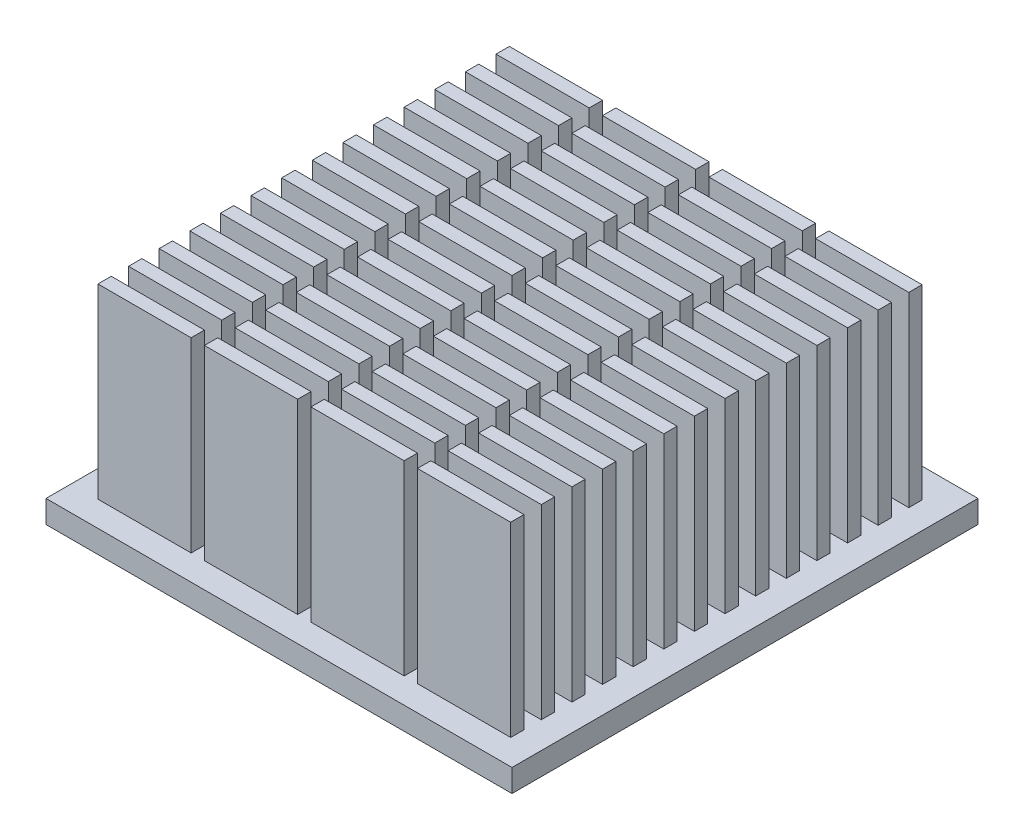
SolidWorks part; units mm, degrees
ref_plane "Front Plane" through (0, 0, 0) normal (0, 0, 1) x (1, 0, 0)
ref_plane "Top Plane" through (0, 0, 0) normal (0, 1, 0) x (1, 0, 0)
ref_plane "Right Plane" through (0, 0, 0) normal (1, 0, 0) x (0, 0, -1)
sketch "Sketch1" plane through (0, 0, 0) normal (0, 1, 0) x (1, 0, 0)
  line L1 (-17.5, -17.5) -> (17.5, -17.5)
  line L2 (-17.5, -17.5) -> (-17.5, 17.5)
  line L3 (-17.5, 17.5) -> (17.5, 17.5)
  line L4 (17.5, -17.5) -> (17.5, 17.5)
  line L5 (-17.5, -17.5) -> (17.5, 17.5) construction
  line L6 (-17.5, 17.5) -> (17.5, -17.5) construction
  point P0 (0, 0)
  dimension "D1" = 35
  dimension "D2" = 35
extrude "Boss-Extrude1" add sketch "Sketch1" along normal blind 1.7
sketch "Sketch2" plane through (0, 1.7, 0) normal (0, 1, 0) x (1, 0, 0)
  line L0 (-15.5, -0.8) -> (-8.5, -0.8)
  line L1 (-15.5, 1.5) -> (-8.5, 1.5)
  line L2 (-15.5, 1.5) -> (-15.5, 0.5)
  line L3 (-15.5, 0.5) -> (-8.5, 0.5)
  line L4 (-8.5, 1.5) -> (-8.5, 0.5)
  line L5 (-7.5, 1.5) -> (-0.5, 1.5)
  line L6 (-7.5, 1.5) -> (-7.5, 0.5)
  line L7 (-7.5, 0.5) -> (-0.5, 0.5)
  line L8 (-0.5, 1.5) -> (-0.5, 0.5)
  line L9 (0.5, 1.5) -> (7.5, 1.5)
  line L10 (0.5, 1.5) -> (0.5, 0.5)
  line L11 (0.5, 0.5) -> (7.5, 0.5)
  line L12 (7.5, 1.5) -> (7.5, 0.5)
  line L13 (8.5, 1.5) -> (15.5, 1.5)
  line L14 (8.5, 1.5) -> (8.5, 0.5)
  line L15 (8.5, 0.5) -> (15.5, 0.5)
  line L16 (15.5, 1.5) -> (15.5, 0.5)
  line L17 (-15.5, -0.8) -> (-15.5, -1.8)
  line L18 (-15.5, -1.8) -> (-8.5, -1.8)
  line L19 (-8.5, -0.8) -> (-8.5, -1.8)
  line L20 (-7.5, -0.8) -> (-0.5, -0.8)
  line L21 (-7.5, -0.8) -> (-7.5, -1.8)
  line L22 (-7.5, -1.8) -> (-0.5, -1.8)
  line L23 (-0.5, -0.8) -> (-0.5, -1.8)
  line L24 (0.5, -0.8) -> (7.5, -0.8)
  line L25 (0.5, -0.8) -> (0.5, -1.8)
  line L26 (0.5, -1.8) -> (7.5, -1.8)
  line L27 (7.5, -0.8) -> (7.5, -1.8)
  line L28 (8.5, -0.8) -> (15.5, -0.8)
  line L29 (8.5, -0.8) -> (8.5, -1.8)
  line L30 (8.5, -1.8) -> (15.5, -1.8)
  line L31 (15.5, -0.8) -> (15.5, -1.8)
  line L32 (-15.5, -3.1) -> (-8.5, -3.1)
  line L33 (-15.5, -3.1) -> (-15.5, -4.1)
  line L34 (-15.5, -4.1) -> (-8.5, -4.1)
  line L35 (-8.5, -3.1) -> (-8.5, -4.1)
  line L36 (-7.5, -3.1) -> (-0.5, -3.1)
  line L37 (-7.5, -3.1) -> (-7.5, -4.1)
  line L38 (-7.5, -4.1) -> (-0.5, -4.1)
  line L39 (-0.5, -3.1) -> (-0.5, -4.1)
  line L40 (0.5, -3.1) -> (7.5, -3.1)
  line L41 (0.5, -3.1) -> (0.5, -4.1)
  line L42 (0.5, -4.1) -> (7.5, -4.1)
  line L43 (7.5, -3.1) -> (7.5, -4.1)
  line L44 (8.5, -3.1) -> (15.5, -3.1)
  line L45 (8.5, -3.1) -> (8.5, -4.1)
  line L46 (8.5, -4.1) -> (15.5, -4.1)
  line L47 (15.5, -3.1) -> (15.5, -4.1)
  line L48 (-15.5, -5.4) -> (-8.5, -5.4)
  line L49 (-15.5, -5.4) -> (-15.5, -6.4)
  line L50 (-15.5, -6.4) -> (-8.5, -6.4)
  line L51 (-8.5, -5.4) -> (-8.5, -6.4)
  line L52 (-7.5, -5.4) -> (-0.5, -5.4)
  line L53 (-7.5, -5.4) -> (-7.5, -6.4)
  line L54 (-7.5, -6.4) -> (-0.5, -6.4)
  line L55 (-0.5, -5.4) -> (-0.5, -6.4)
  line L56 (0.5, -5.4) -> (7.5, -5.4)
  line L57 (0.5, -5.4) -> (0.5, -6.4)
  line L58 (0.5, -6.4) -> (7.5, -6.4)
  line L59 (7.5, -5.4) -> (7.5, -6.4)
  line L60 (8.5, -5.4) -> (15.5, -5.4)
  line L61 (8.5, -5.4) -> (8.5, -6.4)
  line L62 (8.5, -6.4) -> (15.5, -6.4)
  line L63 (15.5, -5.4) -> (15.5, -6.4)
  line L64 (-15.5, -7.7) -> (-8.5, -7.7)
  line L65 (-15.5, -7.7) -> (-15.5, -8.7)
  line L66 (-15.5, -8.7) -> (-8.5, -8.7)
  line L67 (-8.5, -7.7) -> (-8.5, -8.7)
  line L68 (-7.5, -7.7) -> (-0.5, -7.7)
  line L69 (-7.5, -7.7) -> (-7.5, -8.7)
  line L70 (-7.5, -8.7) -> (-0.5, -8.7)
  line L71 (-0.5, -7.7) -> (-0.5, -8.7)
  line L72 (0.5, -7.7) -> (7.5, -7.7)
  line L73 (0.5, -7.7) -> (0.5, -8.7)
  line L74 (0.5, -8.7) -> (7.5, -8.7)
  line L75 (7.5, -7.7) -> (7.5, -8.7)
  line L76 (8.5, -7.7) -> (15.5, -7.7)
  line L77 (8.5, -7.7) -> (8.5, -8.7)
  line L78 (8.5, -8.7) -> (15.5, -8.7)
  line L79 (15.5, -7.7) -> (15.5, -8.7)
  line L80 (-15.5, -10) -> (-8.5, -10)
  line L81 (-15.5, -10) -> (-15.5, -11)
  line L82 (-15.5, -11) -> (-8.5, -11)
  line L83 (-8.5, -10) -> (-8.5, -11)
  line L84 (-7.5, -10) -> (-0.5, -10)
  line L85 (-7.5, -10) -> (-7.5, -11)
  line L86 (-7.5, -11) -> (-0.5, -11)
  line L87 (-0.5, -10) -> (-0.5, -11)
  line L88 (0.5, -10) -> (7.5, -10)
  line L89 (0.5, -10) -> (0.5, -11)
  line L90 (0.5, -11) -> (7.5, -11)
  line L91 (7.5, -10) -> (7.5, -11)
  line L92 (8.5, -10) -> (15.5, -10)
  line L93 (8.5, -10) -> (8.5, -11)
  line L94 (8.5, -11) -> (15.5, -11)
  line L95 (15.5, -10) -> (15.5, -11)
  line L96 (-15.5, -12.3) -> (-8.5, -12.3)
  line L97 (-15.5, -12.3) -> (-15.5, -13.3)
  line L98 (-15.5, -13.3) -> (-8.5, -13.3)
  line L99 (-8.5, -12.3) -> (-8.5, -13.3)
  line L100 (-7.5, -12.3) -> (-0.5, -12.3)
  line L101 (-7.5, -12.3) -> (-7.5, -13.3)
  line L102 (-7.5, -13.3) -> (-0.5, -13.3)
  line L103 (-0.5, -12.3) -> (-0.5, -13.3)
  line L104 (0.5, -12.3) -> (7.5, -12.3)
  line L105 (0.5, -12.3) -> (0.5, -13.3)
  line L106 (0.5, -13.3) -> (7.5, -13.3)
  line L107 (7.5, -12.3) -> (7.5, -13.3)
  line L108 (8.5, -12.3) -> (15.5, -12.3)
  line L109 (8.5, -12.3) -> (8.5, -13.3)
  line L110 (8.5, -13.3) -> (15.5, -13.3)
  line L111 (15.5, -12.3) -> (15.5, -13.3)
  line L112 (-15.5, -14.6) -> (-8.5, -14.6)
  line L113 (-15.5, -14.6) -> (-15.5, -15.6)
  line L114 (-15.5, -15.6) -> (-8.5, -15.6)
  line L115 (-8.5, -14.6) -> (-8.5, -15.6)
  line L116 (-7.5, -14.6) -> (-0.5, -14.6)
  line L117 (-7.5, -14.6) -> (-7.5, -15.6)
  line L118 (-7.5, -15.6) -> (-0.5, -15.6)
  line L119 (-0.5, -14.6) -> (-0.5, -15.6)
  line L120 (0.5, -14.6) -> (7.5, -14.6)
  line L121 (0.5, -14.6) -> (0.5, -15.6)
  line L122 (0.5, -15.6) -> (7.5, -15.6)
  line L123 (7.5, -14.6) -> (7.5, -15.6)
  line L124 (8.5, -14.6) -> (15.5, -14.6)
  line L125 (8.5, -14.6) -> (8.5, -15.6)
  line L126 (8.5, -15.6) -> (15.5, -15.6)
  line L127 (15.5, -14.6) -> (15.5, -15.6)
  line L128 (-15.5, 1.5) -> (-8.5, 1.5)
  line L129 (-15.5, 1.5) -> (-15.5, 0.5)
  line L130 (-15.5, 0.5) -> (-8.5, 0.5)
  line L131 (-8.5, 1.5) -> (-8.5, 0.5)
  line L132 (-7.5, 1.5) -> (-0.5, 1.5)
  line L133 (-7.5, 1.5) -> (-7.5, 0.5)
  line L134 (-7.5, 0.5) -> (-0.5, 0.5)
  line L135 (-0.5, 1.5) -> (-0.5, 0.5)
  line L136 (0.5, 1.5) -> (7.5, 1.5)
  line L137 (0.5, 1.5) -> (0.5, 0.5)
  line L138 (0.5, 0.5) -> (7.5, 0.5)
  line L139 (7.5, 1.5) -> (7.5, 0.5)
  line L140 (8.5, 1.5) -> (15.5, 1.5)
  line L141 (8.5, 1.5) -> (8.5, 0.5)
  line L142 (8.5, 0.5) -> (15.5, 0.5)
  line L143 (15.5, 1.5) -> (15.5, 0.5)
  line L144 (-15.5, -0.8) -> (-8.5, -0.8)
  line L145 (-15.5, -0.8) -> (-15.5, -1.8)
  line L146 (-15.5, -1.8) -> (-8.5, -1.8)
  line L147 (-8.5, -0.8) -> (-8.5, -1.8)
  line L148 (-7.5, -0.8) -> (-0.5, -0.8)
  line L149 (-7.5, -0.8) -> (-7.5, -1.8)
  line L150 (-7.5, -1.8) -> (-0.5, -1.8)
  line L151 (-0.5, -0.8) -> (-0.5, -1.8)
  line L152 (0.5, -0.8) -> (7.5, -0.8)
  line L153 (0.5, -0.8) -> (0.5, -1.8)
  line L154 (0.5, -1.8) -> (7.5, -1.8)
  line L155 (7.5, -0.8) -> (7.5, -1.8)
  line L156 (8.5, -0.8) -> (15.5, -0.8)
  line L157 (8.5, -0.8) -> (8.5, -1.8)
  line L158 (8.5, -1.8) -> (15.5, -1.8)
  line L159 (15.5, -0.8) -> (15.5, -1.8)
  line L160 (-15.5, -3.1) -> (-8.5, -3.1)
  line L161 (-15.5, -3.1) -> (-15.5, -4.1)
  line L162 (-15.5, -4.1) -> (-8.5, -4.1)
  line L163 (-8.5, -3.1) -> (-8.5, -4.1)
  line L164 (-7.5, -3.1) -> (-0.5, -3.1)
  line L165 (-7.5, -3.1) -> (-7.5, -4.1)
  line L166 (-7.5, -4.1) -> (-0.5, -4.1)
  line L167 (-0.5, -3.1) -> (-0.5, -4.1)
  line L168 (0.5, -3.1) -> (7.5, -3.1)
  line L169 (0.5, -3.1) -> (0.5, -4.1)
  line L170 (0.5, -4.1) -> (7.5, -4.1)
  line L171 (7.5, -3.1) -> (7.5, -4.1)
  line L172 (8.5, -3.1) -> (15.5, -3.1)
  line L173 (8.5, -3.1) -> (8.5, -4.1)
  line L174 (8.5, -4.1) -> (15.5, -4.1)
  line L175 (15.5, -3.1) -> (15.5, -4.1)
  line L176 (-15.5, -5.4) -> (-8.5, -5.4)
  line L177 (-15.5, -5.4) -> (-15.5, -6.4)
  line L178 (-15.5, -6.4) -> (-8.5, -6.4)
  line L179 (-8.5, -5.4) -> (-8.5, -6.4)
  line L180 (-7.5, -5.4) -> (-0.5, -5.4)
  line L181 (-7.5, -5.4) -> (-7.5, -6.4)
  line L182 (-7.5, -6.4) -> (-0.5, -6.4)
  line L183 (-0.5, -5.4) -> (-0.5, -6.4)
  line L184 (0.5, -5.4) -> (7.5, -5.4)
  line L185 (0.5, -5.4) -> (0.5, -6.4)
  line L186 (0.5, -6.4) -> (7.5, -6.4)
  line L187 (7.5, -5.4) -> (7.5, -6.4)
  line L188 (8.5, -5.4) -> (15.5, -5.4)
  line L189 (8.5, -5.4) -> (8.5, -6.4)
  line L190 (8.5, -6.4) -> (15.5, -6.4)
  line L191 (15.5, -5.4) -> (15.5, -6.4)
  line L192 (-15.5, -7.7) -> (-8.5, -7.7)
  line L193 (-15.5, -7.7) -> (-15.5, -8.7)
  line L194 (-15.5, -8.7) -> (-8.5, -8.7)
  line L195 (-8.5, -7.7) -> (-8.5, -8.7)
  line L196 (-7.5, -7.7) -> (-0.5, -7.7)
  line L197 (-7.5, -7.7) -> (-7.5, -8.7)
  line L198 (-7.5, -8.7) -> (-0.5, -8.7)
  line L199 (-0.5, -7.7) -> (-0.5, -8.7)
  line L200 (0.5, -7.7) -> (7.5, -7.7)
  line L201 (0.5, -7.7) -> (0.5, -8.7)
  line L202 (0.5, -8.7) -> (7.5, -8.7)
  line L203 (7.5, -7.7) -> (7.5, -8.7)
  line L204 (8.5, -7.7) -> (15.5, -7.7)
  line L205 (8.5, -7.7) -> (8.5, -8.7)
  line L206 (8.5, -8.7) -> (15.5, -8.7)
  line L207 (15.5, -7.7) -> (15.5, -8.7)
  line L208 (-15.5, -10) -> (-8.5, -10)
  line L209 (-15.5, -10) -> (-15.5, -11)
  line L210 (-15.5, -11) -> (-8.5, -11)
  line L211 (-8.5, -10) -> (-8.5, -11)
  line L212 (-7.5, -10) -> (-0.5, -10)
  line L213 (-7.5, -10) -> (-7.5, -11)
  line L214 (-7.5, -11) -> (-0.5, -11)
  line L215 (-0.5, -10) -> (-0.5, -11)
  line L216 (0.5, -10) -> (7.5, -10)
  line L217 (0.5, -10) -> (0.5, -11)
  line L218 (0.5, -11) -> (7.5, -11)
  line L219 (7.5, -10) -> (7.5, -11)
  line L220 (8.5, -10) -> (15.5, -10)
  line L221 (8.5, -10) -> (8.5, -11)
  line L222 (8.5, -11) -> (15.5, -11)
  line L223 (15.5, -10) -> (15.5, -11)
  line L224 (-15.5, -12.3) -> (-8.5, -12.3)
  line L225 (-15.5, -12.3) -> (-15.5, -13.3)
  line L226 (-15.5, -13.3) -> (-8.5, -13.3)
  line L227 (-8.5, -12.3) -> (-8.5, -13.3)
  line L228 (-7.5, -12.3) -> (-0.5, -12.3)
  line L229 (-7.5, -12.3) -> (-7.5, -13.3)
  line L230 (-7.5, -13.3) -> (-0.5, -13.3)
  line L231 (-0.5, -12.3) -> (-0.5, -13.3)
  line L232 (0.5, -12.3) -> (7.5, -12.3)
  line L233 (0.5, -12.3) -> (0.5, -13.3)
  line L234 (0.5, -13.3) -> (7.5, -13.3)
  line L235 (7.5, -12.3) -> (7.5, -13.3)
  line L236 (8.5, -12.3) -> (15.5, -12.3)
  line L237 (8.5, -12.3) -> (8.5, -13.3)
  line L238 (8.5, -13.3) -> (15.5, -13.3)
  line L239 (15.5, -12.3) -> (15.5, -13.3)
  line L240 (-15.5, 3.8) -> (-8.5, 3.8)
  line L241 (-15.5, 3.8) -> (-15.5, 2.8)
  line L242 (-15.5, 2.8) -> (-8.5, 2.8)
  line L243 (-8.5, 3.8) -> (-8.5, 2.8)
  line L244 (-7.5, 3.8) -> (-0.5, 3.8)
  line L245 (-7.5, 3.8) -> (-7.5, 2.8)
  line L246 (-7.5, 2.8) -> (-0.5, 2.8)
  line L247 (-0.5, 3.8) -> (-0.5, 2.8)
  line L248 (0.5, 3.8) -> (7.5, 3.8)
  line L249 (0.5, 3.8) -> (0.5, 2.8)
  line L250 (0.5, 2.8) -> (7.5, 2.8)
  line L251 (7.5, 3.8) -> (7.5, 2.8)
  line L252 (8.5, 3.8) -> (15.5, 3.8)
  line L253 (8.5, 3.8) -> (8.5, 2.8)
  line L254 (8.5, 2.8) -> (15.5, 2.8)
  line L255 (15.5, 3.8) -> (15.5, 2.8)
  line L256 (-15.5, 1.5) -> (-8.5, 1.5)
  line L257 (-15.5, 1.5) -> (-15.5, 0.5)
  line L258 (-15.5, 0.5) -> (-8.5, 0.5)
  line L259 (-8.5, 1.5) -> (-8.5, 0.5)
  line L260 (-7.5, 1.5) -> (-0.5, 1.5)
  line L261 (-7.5, 1.5) -> (-7.5, 0.5)
  line L262 (-7.5, 0.5) -> (-0.5, 0.5)
  line L263 (-0.5, 1.5) -> (-0.5, 0.5)
  line L264 (0.5, 1.5) -> (7.5, 1.5)
  line L265 (0.5, 1.5) -> (0.5, 0.5)
  line L266 (0.5, 0.5) -> (7.5, 0.5)
  line L267 (7.5, 1.5) -> (7.5, 0.5)
  line L268 (8.5, 1.5) -> (15.5, 1.5)
  line L269 (8.5, 1.5) -> (8.5, 0.5)
  line L270 (8.5, 0.5) -> (15.5, 0.5)
  line L271 (15.5, 1.5) -> (15.5, 0.5)
  line L272 (-15.5, -0.8) -> (-8.5, -0.8)
  line L273 (-15.5, -0.8) -> (-15.5, -1.8)
  line L274 (-15.5, -1.8) -> (-8.5, -1.8)
  line L275 (-8.5, -0.8) -> (-8.5, -1.8)
  line L276 (-7.5, -0.8) -> (-0.5, -0.8)
  line L277 (-7.5, -0.8) -> (-7.5, -1.8)
  line L278 (-7.5, -1.8) -> (-0.5, -1.8)
  line L279 (-0.5, -0.8) -> (-0.5, -1.8)
  line L280 (0.5, -0.8) -> (7.5, -0.8)
  line L281 (0.5, -0.8) -> (0.5, -1.8)
  line L282 (0.5, -1.8) -> (7.5, -1.8)
  line L283 (7.5, -0.8) -> (7.5, -1.8)
  line L284 (8.5, -0.8) -> (15.5, -0.8)
  line L285 (8.5, -0.8) -> (8.5, -1.8)
  line L286 (8.5, -1.8) -> (15.5, -1.8)
  line L287 (15.5, -0.8) -> (15.5, -1.8)
  line L288 (-15.5, -3.1) -> (-8.5, -3.1)
  line L289 (-15.5, -3.1) -> (-15.5, -4.1)
  line L290 (-15.5, -4.1) -> (-8.5, -4.1)
  line L291 (-8.5, -3.1) -> (-8.5, -4.1)
  line L292 (-7.5, -3.1) -> (-0.5, -3.1)
  line L293 (-7.5, -3.1) -> (-7.5, -4.1)
  line L294 (-7.5, -4.1) -> (-0.5, -4.1)
  line L295 (-0.5, -3.1) -> (-0.5, -4.1)
  line L296 (0.5, -3.1) -> (7.5, -3.1)
  line L297 (0.5, -3.1) -> (0.5, -4.1)
  line L298 (0.5, -4.1) -> (7.5, -4.1)
  line L299 (7.5, -3.1) -> (7.5, -4.1)
  line L300 (8.5, -3.1) -> (15.5, -3.1)
  line L301 (8.5, -3.1) -> (8.5, -4.1)
  line L302 (8.5, -4.1) -> (15.5, -4.1)
  line L303 (15.5, -3.1) -> (15.5, -4.1)
  line L304 (-15.5, -5.4) -> (-8.5, -5.4)
  line L305 (-15.5, -5.4) -> (-15.5, -6.4)
  line L306 (-15.5, -6.4) -> (-8.5, -6.4)
  line L307 (-8.5, -5.4) -> (-8.5, -6.4)
  line L308 (-7.5, -5.4) -> (-0.5, -5.4)
  line L309 (-7.5, -5.4) -> (-7.5, -6.4)
  line L310 (-7.5, -6.4) -> (-0.5, -6.4)
  line L311 (-0.5, -5.4) -> (-0.5, -6.4)
  line L312 (0.5, -5.4) -> (7.5, -5.4)
  line L313 (0.5, -5.4) -> (0.5, -6.4)
  line L314 (0.5, -6.4) -> (7.5, -6.4)
  line L315 (7.5, -5.4) -> (7.5, -6.4)
  line L316 (8.5, -5.4) -> (15.5, -5.4)
  line L317 (8.5, -5.4) -> (8.5, -6.4)
  line L318 (8.5, -6.4) -> (15.5, -6.4)
  line L319 (15.5, -5.4) -> (15.5, -6.4)
  line L320 (-15.5, -7.7) -> (-8.5, -7.7)
  line L321 (-15.5, -7.7) -> (-15.5, -8.7)
  line L322 (-15.5, -8.7) -> (-8.5, -8.7)
  line L323 (-8.5, -7.7) -> (-8.5, -8.7)
  line L324 (-7.5, -7.7) -> (-0.5, -7.7)
  line L325 (-7.5, -7.7) -> (-7.5, -8.7)
  line L326 (-7.5, -8.7) -> (-0.5, -8.7)
  line L327 (-0.5, -7.7) -> (-0.5, -8.7)
  line L328 (0.5, -7.7) -> (7.5, -7.7)
  line L329 (0.5, -7.7) -> (0.5, -8.7)
  line L330 (0.5, -8.7) -> (7.5, -8.7)
  line L331 (7.5, -7.7) -> (7.5, -8.7)
  line L332 (8.5, -7.7) -> (15.5, -7.7)
  line L333 (8.5, -7.7) -> (8.5, -8.7)
  line L334 (8.5, -8.7) -> (15.5, -8.7)
  line L335 (15.5, -7.7) -> (15.5, -8.7)
  line L336 (-15.5, -10) -> (-8.5, -10)
  line L337 (-15.5, -10) -> (-15.5, -11)
  line L338 (-15.5, -11) -> (-8.5, -11)
  line L339 (-8.5, -10) -> (-8.5, -11)
  line L340 (-7.5, -10) -> (-0.5, -10)
  line L341 (-7.5, -10) -> (-7.5, -11)
  line L342 (-7.5, -11) -> (-0.5, -11)
  line L343 (-0.5, -10) -> (-0.5, -11)
  line L344 (0.5, -10) -> (7.5, -10)
  line L345 (0.5, -10) -> (0.5, -11)
  line L346 (0.5, -11) -> (7.5, -11)
  line L347 (7.5, -10) -> (7.5, -11)
  line L348 (8.5, -10) -> (15.5, -10)
  line L349 (8.5, -10) -> (8.5, -11)
  line L350 (8.5, -11) -> (15.5, -11)
  line L351 (15.5, -10) -> (15.5, -11)
  line L352 (-15.5, 6.1) -> (-8.5, 6.1)
  line L353 (-15.5, 6.1) -> (-15.5, 5.1)
  line L354 (-15.5, 5.1) -> (-8.5, 5.1)
  line L355 (-8.5, 6.1) -> (-8.5, 5.1)
  line L356 (-7.5, 6.1) -> (-0.5, 6.1)
  line L357 (-7.5, 6.1) -> (-7.5, 5.1)
  line L358 (-7.5, 5.1) -> (-0.5, 5.1)
  line L359 (-0.5, 6.1) -> (-0.5, 5.1)
  line L360 (0.5, 6.1) -> (7.5, 6.1)
  line L361 (0.5, 6.1) -> (0.5, 5.1)
  line L362 (0.5, 5.1) -> (7.5, 5.1)
  line L363 (7.5, 6.1) -> (7.5, 5.1)
  line L364 (8.5, 6.1) -> (15.5, 6.1)
  line L365 (8.5, 6.1) -> (8.5, 5.1)
  line L366 (8.5, 5.1) -> (15.5, 5.1)
  line L367 (15.5, 6.1) -> (15.5, 5.1)
  line L368 (-15.5, 3.8) -> (-8.5, 3.8)
  line L369 (-15.5, 3.8) -> (-15.5, 2.8)
  line L370 (-15.5, 2.8) -> (-8.5, 2.8)
  line L371 (-8.5, 3.8) -> (-8.5, 2.8)
  line L372 (-7.5, 3.8) -> (-0.5, 3.8)
  line L373 (-7.5, 3.8) -> (-7.5, 2.8)
  line L374 (-7.5, 2.8) -> (-0.5, 2.8)
  line L375 (-0.5, 3.8) -> (-0.5, 2.8)
  line L376 (0.5, 3.8) -> (7.5, 3.8)
  line L377 (0.5, 3.8) -> (0.5, 2.8)
  line L378 (0.5, 2.8) -> (7.5, 2.8)
  line L379 (7.5, 3.8) -> (7.5, 2.8)
  line L380 (8.5, 3.8) -> (15.5, 3.8)
  line L381 (8.5, 3.8) -> (8.5, 2.8)
  line L382 (8.5, 2.8) -> (15.5, 2.8)
  line L383 (15.5, 3.8) -> (15.5, 2.8)
  line L384 (-15.5, 1.5) -> (-8.5, 1.5)
  line L385 (-15.5, 1.5) -> (-15.5, 0.5)
  line L386 (-15.5, 0.5) -> (-8.5, 0.5)
  line L387 (-8.5, 1.5) -> (-8.5, 0.5)
  line L388 (-7.5, 1.5) -> (-0.5, 1.5)
  line L389 (-7.5, 1.5) -> (-7.5, 0.5)
  line L390 (-7.5, 0.5) -> (-0.5, 0.5)
  line L391 (-0.5, 1.5) -> (-0.5, 0.5)
  line L392 (0.5, 1.5) -> (7.5, 1.5)
  line L393 (0.5, 1.5) -> (0.5, 0.5)
  line L394 (0.5, 0.5) -> (7.5, 0.5)
  line L395 (7.5, 1.5) -> (7.5, 0.5)
  line L396 (8.5, 1.5) -> (15.5, 1.5)
  line L397 (8.5, 1.5) -> (8.5, 0.5)
  line L398 (8.5, 0.5) -> (15.5, 0.5)
  line L399 (15.5, 1.5) -> (15.5, 0.5)
  line L400 (-15.5, -0.8) -> (-8.5, -0.8)
  line L401 (-15.5, -0.8) -> (-15.5, -1.8)
  line L402 (-15.5, -1.8) -> (-8.5, -1.8)
  line L403 (-8.5, -0.8) -> (-8.5, -1.8)
  line L404 (-7.5, -0.8) -> (-0.5, -0.8)
  line L405 (-7.5, -0.8) -> (-7.5, -1.8)
  line L406 (-7.5, -1.8) -> (-0.5, -1.8)
  line L407 (-0.5, -0.8) -> (-0.5, -1.8)
  line L408 (0.5, -0.8) -> (7.5, -0.8)
  line L409 (0.5, -0.8) -> (0.5, -1.8)
  line L410 (0.5, -1.8) -> (7.5, -1.8)
  line L411 (7.5, -0.8) -> (7.5, -1.8)
  line L412 (8.5, -0.8) -> (15.5, -0.8)
  line L413 (8.5, -0.8) -> (8.5, -1.8)
  line L414 (8.5, -1.8) -> (15.5, -1.8)
  line L415 (15.5, -0.8) -> (15.5, -1.8)
  line L416 (-15.5, -3.1) -> (-8.5, -3.1)
  line L417 (-15.5, -3.1) -> (-15.5, -4.1)
  line L418 (-15.5, -4.1) -> (-8.5, -4.1)
  line L419 (-8.5, -3.1) -> (-8.5, -4.1)
  line L420 (-7.5, -3.1) -> (-0.5, -3.1)
  line L421 (-7.5, -3.1) -> (-7.5, -4.1)
  line L422 (-7.5, -4.1) -> (-0.5, -4.1)
  line L423 (-0.5, -3.1) -> (-0.5, -4.1)
  line L424 (0.5, -3.1) -> (7.5, -3.1)
  line L425 (0.5, -3.1) -> (0.5, -4.1)
  line L426 (0.5, -4.1) -> (7.5, -4.1)
  line L427 (7.5, -3.1) -> (7.5, -4.1)
  line L428 (8.5, -3.1) -> (15.5, -3.1)
  line L429 (8.5, -3.1) -> (8.5, -4.1)
  line L430 (8.5, -4.1) -> (15.5, -4.1)
  line L431 (15.5, -3.1) -> (15.5, -4.1)
  line L432 (-15.5, -5.4) -> (-8.5, -5.4)
  line L433 (-15.5, -5.4) -> (-15.5, -6.4)
  line L434 (-15.5, -6.4) -> (-8.5, -6.4)
  line L435 (-8.5, -5.4) -> (-8.5, -6.4)
  line L436 (-7.5, -5.4) -> (-0.5, -5.4)
  line L437 (-7.5, -5.4) -> (-7.5, -6.4)
  line L438 (-7.5, -6.4) -> (-0.5, -6.4)
  line L439 (-0.5, -5.4) -> (-0.5, -6.4)
  line L440 (0.5, -5.4) -> (7.5, -5.4)
  line L441 (0.5, -5.4) -> (0.5, -6.4)
  line L442 (0.5, -6.4) -> (7.5, -6.4)
  line L443 (7.5, -5.4) -> (7.5, -6.4)
  line L444 (8.5, -5.4) -> (15.5, -5.4)
  line L445 (8.5, -5.4) -> (8.5, -6.4)
  line L446 (8.5, -6.4) -> (15.5, -6.4)
  line L447 (15.5, -5.4) -> (15.5, -6.4)
  line L448 (-15.5, -7.7) -> (-8.5, -7.7)
  line L449 (-15.5, -7.7) -> (-15.5, -8.7)
  line L450 (-15.5, -8.7) -> (-8.5, -8.7)
  line L451 (-8.5, -7.7) -> (-8.5, -8.7)
  line L452 (-7.5, -7.7) -> (-0.5, -7.7)
  line L453 (-7.5, -7.7) -> (-7.5, -8.7)
  line L454 (-7.5, -8.7) -> (-0.5, -8.7)
  line L455 (-0.5, -7.7) -> (-0.5, -8.7)
  line L456 (0.5, -7.7) -> (7.5, -7.7)
  line L457 (0.5, -7.7) -> (0.5, -8.7)
  line L458 (0.5, -8.7) -> (7.5, -8.7)
  line L459 (7.5, -7.7) -> (7.5, -8.7)
  line L460 (8.5, -7.7) -> (15.5, -7.7)
  line L461 (8.5, -7.7) -> (8.5, -8.7)
  line L462 (8.5, -8.7) -> (15.5, -8.7)
  line L463 (15.5, -7.7) -> (15.5, -8.7)
  line L464 (-15.5, 8.4) -> (-8.5, 8.4)
  line L465 (-15.5, 8.4) -> (-15.5, 7.4)
  line L466 (-15.5, 7.4) -> (-8.5, 7.4)
  line L467 (-8.5, 8.4) -> (-8.5, 7.4)
  line L468 (-7.5, 8.4) -> (-0.5, 8.4)
  line L469 (-7.5, 8.4) -> (-7.5, 7.4)
  line L470 (-7.5, 7.4) -> (-0.5, 7.4)
  line L471 (-0.5, 8.4) -> (-0.5, 7.4)
  line L472 (0.5, 8.4) -> (7.5, 8.4)
  line L473 (0.5, 8.4) -> (0.5, 7.4)
  line L474 (0.5, 7.4) -> (7.5, 7.4)
  line L475 (7.5, 8.4) -> (7.5, 7.4)
  line L476 (8.5, 8.4) -> (15.5, 8.4)
  line L477 (8.5, 8.4) -> (8.5, 7.4)
  line L478 (8.5, 7.4) -> (15.5, 7.4)
  line L479 (15.5, 8.4) -> (15.5, 7.4)
  line L480 (-15.5, 6.1) -> (-8.5, 6.1)
  line L481 (-15.5, 6.1) -> (-15.5, 5.1)
  line L482 (-15.5, 5.1) -> (-8.5, 5.1)
  line L483 (-8.5, 6.1) -> (-8.5, 5.1)
  line L484 (-7.5, 6.1) -> (-0.5, 6.1)
  line L485 (-7.5, 6.1) -> (-7.5, 5.1)
  line L486 (-7.5, 5.1) -> (-0.5, 5.1)
  line L487 (-0.5, 6.1) -> (-0.5, 5.1)
  line L488 (0.5, 6.1) -> (7.5, 6.1)
  line L489 (0.5, 6.1) -> (0.5, 5.1)
  line L490 (0.5, 5.1) -> (7.5, 5.1)
  line L491 (7.5, 6.1) -> (7.5, 5.1)
  line L492 (8.5, 6.1) -> (15.5, 6.1)
  line L493 (8.5, 6.1) -> (8.5, 5.1)
  line L494 (8.5, 5.1) -> (15.5, 5.1)
  line L495 (15.5, 6.1) -> (15.5, 5.1)
  line L496 (-15.5, 3.8) -> (-8.5, 3.8)
  line L497 (-15.5, 3.8) -> (-15.5, 2.8)
  line L498 (-15.5, 2.8) -> (-8.5, 2.8)
  line L499 (-8.5, 3.8) -> (-8.5, 2.8)
  line L500 (-7.5, 3.8) -> (-0.5, 3.8)
  line L501 (-7.5, 3.8) -> (-7.5, 2.8)
  line L502 (-7.5, 2.8) -> (-0.5, 2.8)
  line L503 (-0.5, 3.8) -> (-0.5, 2.8)
  line L504 (0.5, 3.8) -> (7.5, 3.8)
  line L505 (0.5, 3.8) -> (0.5, 2.8)
  line L506 (0.5, 2.8) -> (7.5, 2.8)
  line L507 (7.5, 3.8) -> (7.5, 2.8)
  line L508 (8.5, 3.8) -> (15.5, 3.8)
  line L509 (8.5, 3.8) -> (8.5, 2.8)
  line L510 (8.5, 2.8) -> (15.5, 2.8)
  line L511 (15.5, 3.8) -> (15.5, 2.8)
  line L512 (-15.5, 1.5) -> (-8.5, 1.5)
  line L513 (-15.5, 1.5) -> (-15.5, 0.5)
  line L514 (-15.5, 0.5) -> (-8.5, 0.5)
  line L515 (-8.5, 1.5) -> (-8.5, 0.5)
  line L516 (-7.5, 1.5) -> (-0.5, 1.5)
  line L517 (-7.5, 1.5) -> (-7.5, 0.5)
  line L518 (-7.5, 0.5) -> (-0.5, 0.5)
  line L519 (-0.5, 1.5) -> (-0.5, 0.5)
  line L520 (0.5, 1.5) -> (7.5, 1.5)
  line L521 (0.5, 1.5) -> (0.5, 0.5)
  line L522 (0.5, 0.5) -> (7.5, 0.5)
  line L523 (7.5, 1.5) -> (7.5, 0.5)
  line L524 (8.5, 1.5) -> (15.5, 1.5)
  line L525 (8.5, 1.5) -> (8.5, 0.5)
  line L526 (8.5, 0.5) -> (15.5, 0.5)
  line L527 (15.5, 1.5) -> (15.5, 0.5)
  line L528 (-15.5, -0.8) -> (-8.5, -0.8)
  line L529 (-15.5, -0.8) -> (-15.5, -1.8)
  line L530 (-15.5, -1.8) -> (-8.5, -1.8)
  line L531 (-8.5, -0.8) -> (-8.5, -1.8)
  line L532 (-7.5, -0.8) -> (-0.5, -0.8)
  line L533 (-7.5, -0.8) -> (-7.5, -1.8)
  line L534 (-7.5, -1.8) -> (-0.5, -1.8)
  line L535 (-0.5, -0.8) -> (-0.5, -1.8)
  line L536 (0.5, -0.8) -> (7.5, -0.8)
  line L537 (0.5, -0.8) -> (0.5, -1.8)
  line L538 (0.5, -1.8) -> (7.5, -1.8)
  line L539 (7.5, -0.8) -> (7.5, -1.8)
  line L540 (8.5, -0.8) -> (15.5, -0.8)
  line L541 (8.5, -0.8) -> (8.5, -1.8)
  line L542 (8.5, -1.8) -> (15.5, -1.8)
  line L543 (15.5, -0.8) -> (15.5, -1.8)
  line L544 (-15.5, -3.1) -> (-8.5, -3.1)
  line L545 (-15.5, -3.1) -> (-15.5, -4.1)
  line L546 (-15.5, -4.1) -> (-8.5, -4.1)
  line L547 (-8.5, -3.1) -> (-8.5, -4.1)
  line L548 (-7.5, -3.1) -> (-0.5, -3.1)
  line L549 (-7.5, -3.1) -> (-7.5, -4.1)
  line L550 (-7.5, -4.1) -> (-0.5, -4.1)
  line L551 (-0.5, -3.1) -> (-0.5, -4.1)
  line L552 (0.5, -3.1) -> (7.5, -3.1)
  line L553 (0.5, -3.1) -> (0.5, -4.1)
  line L554 (0.5, -4.1) -> (7.5, -4.1)
  line L555 (7.5, -3.1) -> (7.5, -4.1)
  line L556 (8.5, -3.1) -> (15.5, -3.1)
  line L557 (8.5, -3.1) -> (8.5, -4.1)
  line L558 (8.5, -4.1) -> (15.5, -4.1)
  line L559 (15.5, -3.1) -> (15.5, -4.1)
  line L560 (-15.5, -5.4) -> (-8.5, -5.4)
  line L561 (-15.5, -5.4) -> (-15.5, -6.4)
  line L562 (-15.5, -6.4) -> (-8.5, -6.4)
  line L563 (-8.5, -5.4) -> (-8.5, -6.4)
  line L564 (-7.5, -5.4) -> (-0.5, -5.4)
  line L565 (-7.5, -5.4) -> (-7.5, -6.4)
  line L566 (-7.5, -6.4) -> (-0.5, -6.4)
  line L567 (-0.5, -5.4) -> (-0.5, -6.4)
  line L568 (0.5, -5.4) -> (7.5, -5.4)
  line L569 (0.5, -5.4) -> (0.5, -6.4)
  line L570 (0.5, -6.4) -> (7.5, -6.4)
  line L571 (7.5, -5.4) -> (7.5, -6.4)
  line L572 (8.5, -5.4) -> (15.5, -5.4)
  line L573 (8.5, -5.4) -> (8.5, -6.4)
  line L574 (8.5, -6.4) -> (15.5, -6.4)
  line L575 (15.5, -5.4) -> (15.5, -6.4)
  line L576 (-15.5, 10.7) -> (-8.5, 10.7)
  line L577 (-15.5, 10.7) -> (-15.5, 9.7)
  line L578 (-15.5, 9.7) -> (-8.5, 9.7)
  line L579 (-8.5, 10.7) -> (-8.5, 9.7)
  line L580 (-7.5, 10.7) -> (-0.5, 10.7)
  line L581 (-7.5, 10.7) -> (-7.5, 9.7)
  line L582 (-7.5, 9.7) -> (-0.5, 9.7)
  line L583 (-0.5, 10.7) -> (-0.5, 9.7)
  line L584 (0.5, 10.7) -> (7.5, 10.7)
  line L585 (0.5, 10.7) -> (0.5, 9.7)
  line L586 (0.5, 9.7) -> (7.5, 9.7)
  line L587 (7.5, 10.7) -> (7.5, 9.7)
  line L588 (8.5, 10.7) -> (15.5, 10.7)
  line L589 (8.5, 10.7) -> (8.5, 9.7)
  line L590 (8.5, 9.7) -> (15.5, 9.7)
  line L591 (15.5, 10.7) -> (15.5, 9.7)
  line L592 (-15.5, 8.4) -> (-8.5, 8.4)
  line L593 (-15.5, 8.4) -> (-15.5, 7.4)
  line L594 (-15.5, 7.4) -> (-8.5, 7.4)
  line L595 (-8.5, 8.4) -> (-8.5, 7.4)
  line L596 (-7.5, 8.4) -> (-0.5, 8.4)
  line L597 (-7.5, 8.4) -> (-7.5, 7.4)
  line L598 (-7.5, 7.4) -> (-0.5, 7.4)
  line L599 (-0.5, 8.4) -> (-0.5, 7.4)
  line L600 (0.5, 8.4) -> (7.5, 8.4)
  line L601 (0.5, 8.4) -> (0.5, 7.4)
  line L602 (0.5, 7.4) -> (7.5, 7.4)
  line L603 (7.5, 8.4) -> (7.5, 7.4)
  line L604 (8.5, 8.4) -> (15.5, 8.4)
  line L605 (8.5, 8.4) -> (8.5, 7.4)
  line L606 (8.5, 7.4) -> (15.5, 7.4)
  line L607 (15.5, 8.4) -> (15.5, 7.4)
  line L608 (-15.5, 6.1) -> (-8.5, 6.1)
  line L609 (-15.5, 6.1) -> (-15.5, 5.1)
  line L610 (-15.5, 5.1) -> (-8.5, 5.1)
  line L611 (-8.5, 6.1) -> (-8.5, 5.1)
  line L612 (-7.5, 6.1) -> (-0.5, 6.1)
  line L613 (-7.5, 6.1) -> (-7.5, 5.1)
  line L614 (-7.5, 5.1) -> (-0.5, 5.1)
  line L615 (-0.5, 6.1) -> (-0.5, 5.1)
  line L616 (0.5, 6.1) -> (7.5, 6.1)
  line L617 (0.5, 6.1) -> (0.5, 5.1)
  line L618 (0.5, 5.1) -> (7.5, 5.1)
  line L619 (7.5, 6.1) -> (7.5, 5.1)
  line L620 (8.5, 6.1) -> (15.5, 6.1)
  line L621 (8.5, 6.1) -> (8.5, 5.1)
  line L622 (8.5, 5.1) -> (15.5, 5.1)
  line L623 (15.5, 6.1) -> (15.5, 5.1)
  line L624 (-15.5, 3.8) -> (-8.5, 3.8)
  line L625 (-15.5, 3.8) -> (-15.5, 2.8)
  line L626 (-15.5, 2.8) -> (-8.5, 2.8)
  line L627 (-8.5, 3.8) -> (-8.5, 2.8)
  line L628 (-7.5, 3.8) -> (-0.5, 3.8)
  line L629 (-7.5, 3.8) -> (-7.5, 2.8)
  line L630 (-7.5, 2.8) -> (-0.5, 2.8)
  line L631 (-0.5, 3.8) -> (-0.5, 2.8)
  line L632 (0.5, 3.8) -> (7.5, 3.8)
  line L633 (0.5, 3.8) -> (0.5, 2.8)
  line L634 (0.5, 2.8) -> (7.5, 2.8)
  line L635 (7.5, 3.8) -> (7.5, 2.8)
  line L636 (8.5, 3.8) -> (15.5, 3.8)
  line L637 (8.5, 3.8) -> (8.5, 2.8)
  line L638 (8.5, 2.8) -> (15.5, 2.8)
  line L639 (15.5, 3.8) -> (15.5, 2.8)
  line L640 (-15.5, 1.5) -> (-8.5, 1.5)
  line L641 (-15.5, 1.5) -> (-15.5, 0.5)
  line L642 (-15.5, 0.5) -> (-8.5, 0.5)
  line L643 (-8.5, 1.5) -> (-8.5, 0.5)
  line L644 (-7.5, 1.5) -> (-0.5, 1.5)
  line L645 (-7.5, 1.5) -> (-7.5, 0.5)
  line L646 (-7.5, 0.5) -> (-0.5, 0.5)
  line L647 (-0.5, 1.5) -> (-0.5, 0.5)
  line L648 (0.5, 1.5) -> (7.5, 1.5)
  line L649 (0.5, 1.5) -> (0.5, 0.5)
  line L650 (0.5, 0.5) -> (7.5, 0.5)
  line L651 (7.5, 1.5) -> (7.5, 0.5)
  line L652 (8.5, 1.5) -> (15.5, 1.5)
  line L653 (8.5, 1.5) -> (8.5, 0.5)
  line L654 (8.5, 0.5) -> (15.5, 0.5)
  line L655 (15.5, 1.5) -> (15.5, 0.5)
  line L656 (-15.5, -0.8) -> (-8.5, -0.8)
  line L657 (-15.5, -0.8) -> (-15.5, -1.8)
  line L658 (-15.5, -1.8) -> (-8.5, -1.8)
  line L659 (-8.5, -0.8) -> (-8.5, -1.8)
  line L660 (-7.5, -0.8) -> (-0.5, -0.8)
  line L661 (-7.5, -0.8) -> (-7.5, -1.8)
  line L662 (-7.5, -1.8) -> (-0.5, -1.8)
  line L663 (-0.5, -0.8) -> (-0.5, -1.8)
  line L664 (0.5, -0.8) -> (7.5, -0.8)
  line L665 (0.5, -0.8) -> (0.5, -1.8)
  line L666 (0.5, -1.8) -> (7.5, -1.8)
  line L667 (7.5, -0.8) -> (7.5, -1.8)
  line L668 (8.5, -0.8) -> (15.5, -0.8)
  line L669 (8.5, -0.8) -> (8.5, -1.8)
  line L670 (8.5, -1.8) -> (15.5, -1.8)
  line L671 (15.5, -0.8) -> (15.5, -1.8)
  line L672 (-15.5, -3.1) -> (-8.5, -3.1)
  line L673 (-15.5, -3.1) -> (-15.5, -4.1)
  line L674 (-15.5, -4.1) -> (-8.5, -4.1)
  line L675 (-8.5, -3.1) -> (-8.5, -4.1)
  line L676 (-7.5, -3.1) -> (-0.5, -3.1)
  line L677 (-7.5, -3.1) -> (-7.5, -4.1)
  line L678 (-7.5, -4.1) -> (-0.5, -4.1)
  line L679 (-0.5, -3.1) -> (-0.5, -4.1)
  line L680 (0.5, -3.1) -> (7.5, -3.1)
  line L681 (0.5, -3.1) -> (0.5, -4.1)
  line L682 (0.5, -4.1) -> (7.5, -4.1)
  line L683 (7.5, -3.1) -> (7.5, -4.1)
  line L684 (8.5, -3.1) -> (15.5, -3.1)
  line L685 (8.5, -3.1) -> (8.5, -4.1)
  line L686 (8.5, -4.1) -> (15.5, -4.1)
  line L687 (15.5, -3.1) -> (15.5, -4.1)
  line L688 (-15.5, 13) -> (-8.5, 13)
  line L689 (-15.5, 13) -> (-15.5, 12)
  line L690 (-15.5, 12) -> (-8.5, 12)
  line L691 (-8.5, 13) -> (-8.5, 12)
  line L692 (-7.5, 13) -> (-0.5, 13)
  line L693 (-7.5, 13) -> (-7.5, 12)
  line L694 (-7.5, 12) -> (-0.5, 12)
  line L695 (-0.5, 13) -> (-0.5, 12)
  line L696 (0.5, 13) -> (7.5, 13)
  line L697 (0.5, 13) -> (0.5, 12)
  line L698 (0.5, 12) -> (7.5, 12)
  line L699 (7.5, 13) -> (7.5, 12)
  line L700 (8.5, 13) -> (15.5, 13)
  line L701 (8.5, 13) -> (8.5, 12)
  line L702 (8.5, 12) -> (15.5, 12)
  line L703 (15.5, 13) -> (15.5, 12)
  line L704 (-15.5, 10.7) -> (-8.5, 10.7)
  line L705 (-15.5, 10.7) -> (-15.5, 9.7)
  line L706 (-15.5, 9.7) -> (-8.5, 9.7)
  line L707 (-8.5, 10.7) -> (-8.5, 9.7)
  line L708 (-7.5, 10.7) -> (-0.5, 10.7)
  line L709 (-7.5, 10.7) -> (-7.5, 9.7)
  line L710 (-7.5, 9.7) -> (-0.5, 9.7)
  line L711 (-0.5, 10.7) -> (-0.5, 9.7)
  line L712 (0.5, 10.7) -> (7.5, 10.7)
  line L713 (0.5, 10.7) -> (0.5, 9.7)
  line L714 (0.5, 9.7) -> (7.5, 9.7)
  line L715 (7.5, 10.7) -> (7.5, 9.7)
  line L716 (8.5, 10.7) -> (15.5, 10.7)
  line L717 (8.5, 10.7) -> (8.5, 9.7)
  line L718 (8.5, 9.7) -> (15.5, 9.7)
  line L719 (15.5, 10.7) -> (15.5, 9.7)
  line L720 (-15.5, 8.4) -> (-8.5, 8.4)
  line L721 (-15.5, 8.4) -> (-15.5, 7.4)
  line L722 (-15.5, 7.4) -> (-8.5, 7.4)
  line L723 (-8.5, 8.4) -> (-8.5, 7.4)
  line L724 (-7.5, 8.4) -> (-0.5, 8.4)
  line L725 (-7.5, 8.4) -> (-7.5, 7.4)
  line L726 (-7.5, 7.4) -> (-0.5, 7.4)
  line L727 (-0.5, 8.4) -> (-0.5, 7.4)
  line L728 (0.5, 8.4) -> (7.5, 8.4)
  line L729 (0.5, 8.4) -> (0.5, 7.4)
  line L730 (0.5, 7.4) -> (7.5, 7.4)
  line L731 (7.5, 8.4) -> (7.5, 7.4)
  line L732 (8.5, 8.4) -> (15.5, 8.4)
  line L733 (8.5, 8.4) -> (8.5, 7.4)
  line L734 (8.5, 7.4) -> (15.5, 7.4)
  line L735 (15.5, 8.4) -> (15.5, 7.4)
  line L736 (-15.5, 6.1) -> (-8.5, 6.1)
  line L737 (-15.5, 6.1) -> (-15.5, 5.1)
  line L738 (-15.5, 5.1) -> (-8.5, 5.1)
  line L739 (-8.5, 6.1) -> (-8.5, 5.1)
  line L740 (-7.5, 6.1) -> (-0.5, 6.1)
  line L741 (-7.5, 6.1) -> (-7.5, 5.1)
  line L742 (-7.5, 5.1) -> (-0.5, 5.1)
  line L743 (-0.5, 6.1) -> (-0.5, 5.1)
  line L744 (0.5, 6.1) -> (7.5, 6.1)
  line L745 (0.5, 6.1) -> (0.5, 5.1)
  line L746 (0.5, 5.1) -> (7.5, 5.1)
  line L747 (7.5, 6.1) -> (7.5, 5.1)
  line L748 (8.5, 6.1) -> (15.5, 6.1)
  line L749 (8.5, 6.1) -> (8.5, 5.1)
  line L750 (8.5, 5.1) -> (15.5, 5.1)
  line L751 (15.5, 6.1) -> (15.5, 5.1)
  line L752 (-15.5, 3.8) -> (-8.5, 3.8)
  line L753 (-15.5, 3.8) -> (-15.5, 2.8)
  line L754 (-15.5, 2.8) -> (-8.5, 2.8)
  line L755 (-8.5, 3.8) -> (-8.5, 2.8)
  line L756 (-7.5, 3.8) -> (-0.5, 3.8)
  line L757 (-7.5, 3.8) -> (-7.5, 2.8)
  line L758 (-7.5, 2.8) -> (-0.5, 2.8)
  line L759 (-0.5, 3.8) -> (-0.5, 2.8)
  line L760 (0.5, 3.8) -> (7.5, 3.8)
  line L761 (0.5, 3.8) -> (0.5, 2.8)
  line L762 (0.5, 2.8) -> (7.5, 2.8)
  line L763 (7.5, 3.8) -> (7.5, 2.8)
  line L764 (8.5, 3.8) -> (15.5, 3.8)
  line L765 (8.5, 3.8) -> (8.5, 2.8)
  line L766 (8.5, 2.8) -> (15.5, 2.8)
  line L767 (15.5, 3.8) -> (15.5, 2.8)
  line L768 (-15.5, 1.5) -> (-8.5, 1.5)
  line L769 (-15.5, 1.5) -> (-15.5, 0.5)
  line L770 (-15.5, 0.5) -> (-8.5, 0.5)
  line L771 (-8.5, 1.5) -> (-8.5, 0.5)
  line L772 (-7.5, 1.5) -> (-0.5, 1.5)
  line L773 (-7.5, 1.5) -> (-7.5, 0.5)
  line L774 (-7.5, 0.5) -> (-0.5, 0.5)
  line L775 (-0.5, 1.5) -> (-0.5, 0.5)
  line L776 (0.5, 1.5) -> (7.5, 1.5)
  line L777 (0.5, 1.5) -> (0.5, 0.5)
  line L778 (0.5, 0.5) -> (7.5, 0.5)
  line L779 (7.5, 1.5) -> (7.5, 0.5)
  line L780 (8.5, 1.5) -> (15.5, 1.5)
  line L781 (8.5, 1.5) -> (8.5, 0.5)
  line L782 (8.5, 0.5) -> (15.5, 0.5)
  line L783 (15.5, 1.5) -> (15.5, 0.5)
  line L784 (-15.5, -0.8) -> (-8.5, -0.8)
  line L785 (-15.5, -0.8) -> (-15.5, -1.8)
  line L786 (-15.5, -1.8) -> (-8.5, -1.8)
  line L787 (-8.5, -0.8) -> (-8.5, -1.8)
  line L788 (-7.5, -0.8) -> (-0.5, -0.8)
  line L789 (-7.5, -0.8) -> (-7.5, -1.8)
  line L790 (-7.5, -1.8) -> (-0.5, -1.8)
  line L791 (-0.5, -0.8) -> (-0.5, -1.8)
  line L792 (0.5, -0.8) -> (7.5, -0.8)
  line L793 (0.5, -0.8) -> (0.5, -1.8)
  line L794 (0.5, -1.8) -> (7.5, -1.8)
  line L795 (7.5, -0.8) -> (7.5, -1.8)
  line L796 (8.5, -0.8) -> (15.5, -0.8)
  line L797 (8.5, -0.8) -> (8.5, -1.8)
  line L798 (8.5, -1.8) -> (15.5, -1.8)
  line L799 (15.5, -0.8) -> (15.5, -1.8)
  line L800 (-15.5, 3.8) -> (-8.5, 3.8)
  line L801 (-15.5, 3.8) -> (-15.5, 2.8)
  line L802 (-15.5, 2.8) -> (-8.5, 2.8)
  line L803 (-8.5, 3.8) -> (-8.5, 2.8)
  line L804 (-7.5, 3.8) -> (-0.5, 3.8)
  line L805 (-7.5, 3.8) -> (-7.5, 2.8)
  line L806 (-7.5, 2.8) -> (-0.5, 2.8)
  line L807 (-0.5, 3.8) -> (-0.5, 2.8)
  line L808 (0.5, 3.8) -> (7.5, 3.8)
  line L809 (0.5, 3.8) -> (0.5, 2.8)
  line L810 (0.5, 2.8) -> (7.5, 2.8)
  line L811 (7.5, 3.8) -> (7.5, 2.8)
  line L812 (8.5, 3.8) -> (15.5, 3.8)
  line L813 (8.5, 3.8) -> (8.5, 2.8)
  line L814 (8.5, 2.8) -> (15.5, 2.8)
  line L815 (15.5, 3.8) -> (15.5, 2.8)
  line L816 (-15.5, 6.1) -> (-8.5, 6.1)
  line L817 (-15.5, 6.1) -> (-15.5, 5.1)
  line L818 (-15.5, 5.1) -> (-8.5, 5.1)
  line L819 (-8.5, 6.1) -> (-8.5, 5.1)
  line L820 (-7.5, 6.1) -> (-0.5, 6.1)
  line L821 (-7.5, 6.1) -> (-7.5, 5.1)
  line L822 (-7.5, 5.1) -> (-0.5, 5.1)
  line L823 (-0.5, 6.1) -> (-0.5, 5.1)
  line L824 (0.5, 6.1) -> (7.5, 6.1)
  line L825 (0.5, 6.1) -> (0.5, 5.1)
  line L826 (0.5, 5.1) -> (7.5, 5.1)
  line L827 (7.5, 6.1) -> (7.5, 5.1)
  line L828 (8.5, 6.1) -> (15.5, 6.1)
  line L829 (8.5, 6.1) -> (8.5, 5.1)
  line L830 (8.5, 5.1) -> (15.5, 5.1)
  line L831 (15.5, 6.1) -> (15.5, 5.1)
  line L832 (-15.5, 8.4) -> (-8.5, 8.4)
  line L833 (-15.5, 8.4) -> (-15.5, 7.4)
  line L834 (-15.5, 7.4) -> (-8.5, 7.4)
  line L835 (-8.5, 8.4) -> (-8.5, 7.4)
  line L836 (-7.5, 8.4) -> (-0.5, 8.4)
  line L837 (-7.5, 8.4) -> (-7.5, 7.4)
  line L838 (-7.5, 7.4) -> (-0.5, 7.4)
  line L839 (-0.5, 8.4) -> (-0.5, 7.4)
  line L840 (0.5, 8.4) -> (7.5, 8.4)
  line L841 (0.5, 8.4) -> (0.5, 7.4)
  line L842 (0.5, 7.4) -> (7.5, 7.4)
  line L843 (7.5, 8.4) -> (7.5, 7.4)
  line L844 (8.5, 8.4) -> (15.5, 8.4)
  line L845 (8.5, 8.4) -> (8.5, 7.4)
  line L846 (8.5, 7.4) -> (15.5, 7.4)
  line L847 (15.5, 8.4) -> (15.5, 7.4)
  line L848 (-15.5, 10.7) -> (-8.5, 10.7)
  line L849 (-15.5, 10.7) -> (-15.5, 9.7)
  line L850 (-15.5, 9.7) -> (-8.5, 9.7)
  line L851 (-8.5, 10.7) -> (-8.5, 9.7)
  line L852 (-7.5, 10.7) -> (-0.5, 10.7)
  line L853 (-7.5, 10.7) -> (-7.5, 9.7)
  line L854 (-7.5, 9.7) -> (-0.5, 9.7)
  line L855 (-0.5, 10.7) -> (-0.5, 9.7)
  line L856 (0.5, 10.7) -> (7.5, 10.7)
  line L857 (0.5, 10.7) -> (0.5, 9.7)
  line L858 (0.5, 9.7) -> (7.5, 9.7)
  line L859 (7.5, 10.7) -> (7.5, 9.7)
  line L860 (8.5, 10.7) -> (15.5, 10.7)
  line L861 (8.5, 10.7) -> (8.5, 9.7)
  line L862 (8.5, 9.7) -> (15.5, 9.7)
  line L863 (15.5, 10.7) -> (15.5, 9.7)
  line L864 (-15.5, 13) -> (-8.5, 13)
  line L865 (-15.5, 13) -> (-15.5, 12)
  line L866 (-15.5, 12) -> (-8.5, 12)
  line L867 (-8.5, 13) -> (-8.5, 12)
  line L868 (-7.5, 13) -> (-0.5, 13)
  line L869 (-7.5, 13) -> (-7.5, 12)
  line L870 (-7.5, 12) -> (-0.5, 12)
  line L871 (-0.5, 13) -> (-0.5, 12)
  line L872 (0.5, 13) -> (7.5, 13)
  line L873 (0.5, 13) -> (0.5, 12)
  line L874 (0.5, 12) -> (7.5, 12)
  line L875 (7.5, 13) -> (7.5, 12)
  line L876 (8.5, 13) -> (15.5, 13)
  line L877 (8.5, 13) -> (8.5, 12)
  line L878 (8.5, 12) -> (15.5, 12)
  line L879 (15.5, 13) -> (15.5, 12)
  line L880 (-15.5, 15.3) -> (-8.5, 15.3)
  line L881 (-15.5, 15.3) -> (-15.5, 14.3)
  line L882 (-15.5, 14.3) -> (-8.5, 14.3)
  line L883 (-8.5, 15.3) -> (-8.5, 14.3)
  line L884 (-7.5, 15.3) -> (-0.5, 15.3)
  line L885 (-7.5, 15.3) -> (-7.5, 14.3)
  line L886 (-7.5, 14.3) -> (-0.5, 14.3)
  line L887 (-0.5, 15.3) -> (-0.5, 14.3)
  line L888 (0.5, 15.3) -> (7.5, 15.3)
  line L889 (0.5, 15.3) -> (0.5, 14.3)
  line L890 (0.5, 14.3) -> (7.5, 14.3)
  line L891 (7.5, 15.3) -> (7.5, 14.3)
  line L892 (8.5, 15.3) -> (15.5, 15.3)
  line L893 (8.5, 15.3) -> (8.5, 14.3)
  line L894 (8.5, 14.3) -> (15.5, 14.3)
  line L895 (15.5, 15.3) -> (15.5, 14.3)
  dimension "D1" = 0.5
  dimension "D2" = 0.5
  dimension "D3" = 1
  dimension "D4" = 1
  dimension "D5" = 7
  dimension "D6" = 7
  dimension "D7" = 7
  dimension "D8" = 7
  dimension "D9" = 1
  dimension "D10" = 1
  dimension "D11" = 1
  dimension "D12" = 1
  dimension "D13" = 0.5
  dimension "D14" = 0.5
  dimension "D15" = 0.5
  dimension "D16" = 0.5
  dimension "D17" = 7
extrude "Boss-Extrude2" add sketch "Sketch2" along normal blind 14
